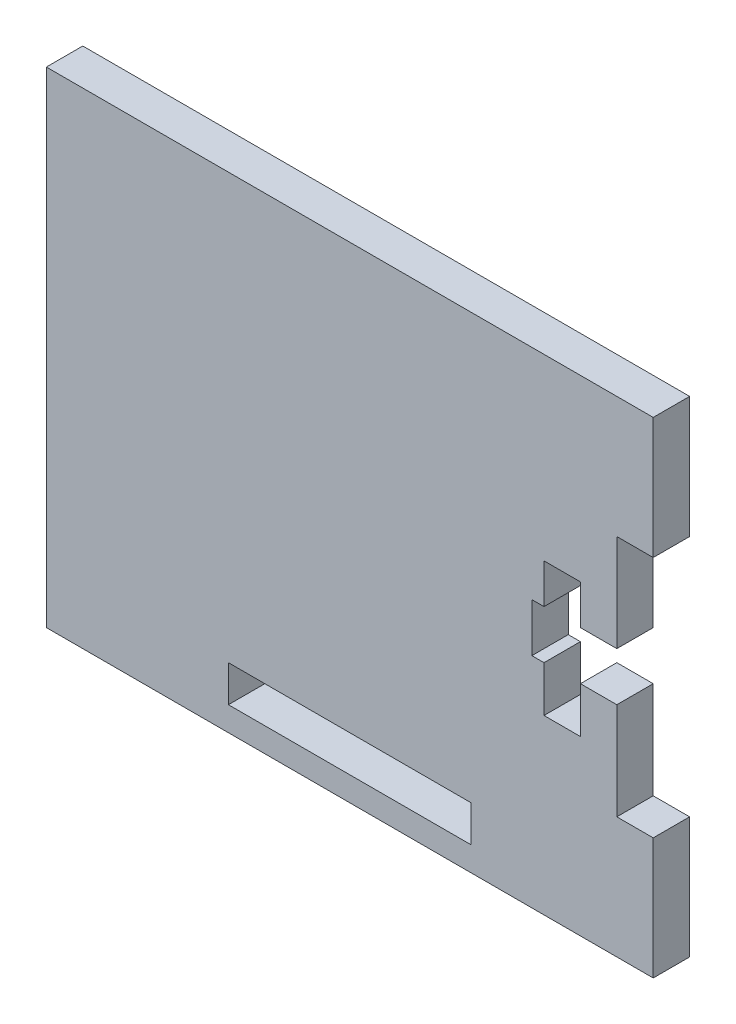
SolidWorks part; units mm, degrees
ref_plane "前视基准面" through (0, 0, 0) normal (0, 0, 1) x (1, 0, 0)
ref_plane "上视基准面" through (0, 0, 0) normal (0, 1, 0) x (1, 0, 0)
ref_plane "右视基准面" through (0, 0, 0) normal (1, 0, 0) x (0, 0, -1)
sketch "草图1" plane through (0, 0, 0) normal (0, 0, 1) x (1, 0, 0)
  line L0 (55, 0) -> (-55, 0) construction
  line L1 (-25, 20) -> (25, 20)
  line L2 (-25, 20) -> (-25, -20)
  line L3 (-25, -20) -> (25, -20)
  line L4 (25, 20) -> (25, 10)
  line L5 (0, -55) -> (0, 55) construction
  line L6 (16, 2) -> (15, 2)
  line L7 (-10, -15) -> (10, -15)
  line L8 (-10, -15) -> (-10, -18)
  line L9 (-10, -18) -> (10, -18)
  line L10 (10, -15) -> (10, -18)
  line L11 (22, 2) -> (19, 2)
  line L13 (22, -2) -> (19, -2)
  line L14 (15, 2) -> (15, -2)
  line L15 (25, 10) -> (22, 10)
  line L17 (25, -10) -> (22, -10)
  line L18 (22, 10) -> (22, 2)
  line L19 (16, 5.2659) -> (19, 5.2659)
  line L20 (16, 5.2659) -> (16, 2)
  line L21 (16, -5.7697) -> (19, -5.7697)
  line L22 (19, 5.2659) -> (19, 2)
  line L23 (16, -2) -> (15, -2)
  line L24 (19, -2) -> (19, -5.7697)
  line L25 (22, -2) -> (22, -10)
  line L26 (16, -2) -> (16, -5.7697)
  line L27 (25, -10) -> (25, -20)
  dimension "D1" = 50
  dimension "D2" = 40
  dimension "D3" = 20
  dimension "D4" = 25
  dimension "D5" = 20
  dimension "D6" = 3
  dimension "D7" = 10
  dimension "D8" = 3
  dimension "D9" = 4
  dimension "D10" = 10
  dimension "D11" = 2
  dimension "D12" = 3
  dimension "D13" = 1
  dimension "D14" = 20
  dimension "D15" = 2
extrude "凸台-拉伸1" add sketch "草图1" along normal mid plane 3
